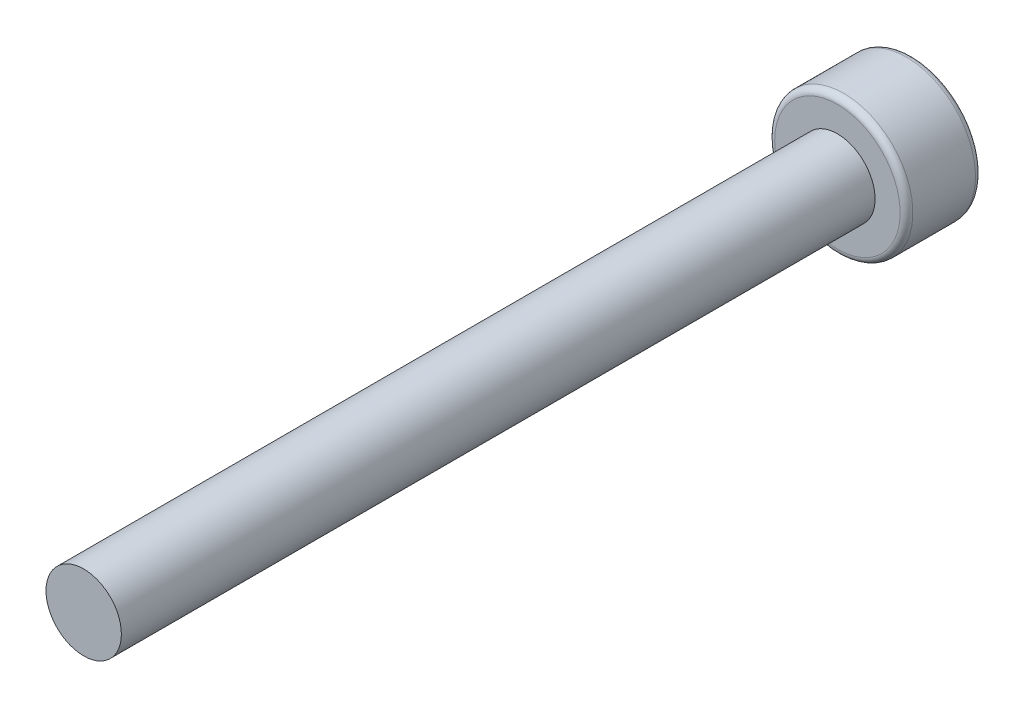
SolidWorks part; units mm, degrees
ref_plane "Front Plane" through (0, 0, 0) normal (0, 0, 1) x (1, 0, 0)
ref_plane "Top Plane" through (0, 0, 0) normal (0, 1, 0) x (1, 0, 0)
ref_plane "Right Plane" through (0, 0, 0) normal (1, 0, 0) x (0, 0, -1)
sketch "Sketch1" plane through (0, 0, 0) normal (0, 0, 1) x (1, 0, 0)
  circle A0 centre (0, 0) radius 1.5
  dimension "D1" = 3
extrude "Boss-Extrude1" add sketch "Sketch1" along normal blind 30
sketch "Sketch2" plane through (0, 0, 0) normal (0, 0, -1) x (-1, 0, 0)
  circle A0 centre (0, 0.0184) radius 2.75
  dimension "D1" = 5.5
extrude "Boss-Extrude2" add sketch "Sketch2" along normal blind 3
fillet "Fillet1" radius 0.254 2 edges at (-2.75, 0.0184, 0) (-2.75, 0.0184, -3)
sketch "Sketch3" plane through (0, 0, -3) normal (0, 0, -1) x (-1, 0, 0)
  line L1 (1.5701, -0.2293) -> (0.9996, 1.2543)
  line L2 (0.9996, 1.2543) -> (-0.5705, 1.5021)
  line L3 (-0.5705, 1.5021) -> (-1.5701, 0.2662)
  line L4 (-1.5701, 0.2662) -> (-0.9996, -1.2175)
  line L5 (-0.9996, -1.2175) -> (0.5705, -1.4652)
  line L6 (0.5705, -1.4652) -> (1.5701, -0.2293)
  circle A0 centre (0, 0.0184) radius 1.3766 construction
extrude "Cut-Extrude1" cut sketch "Sketch3" against normal blind 2.54
